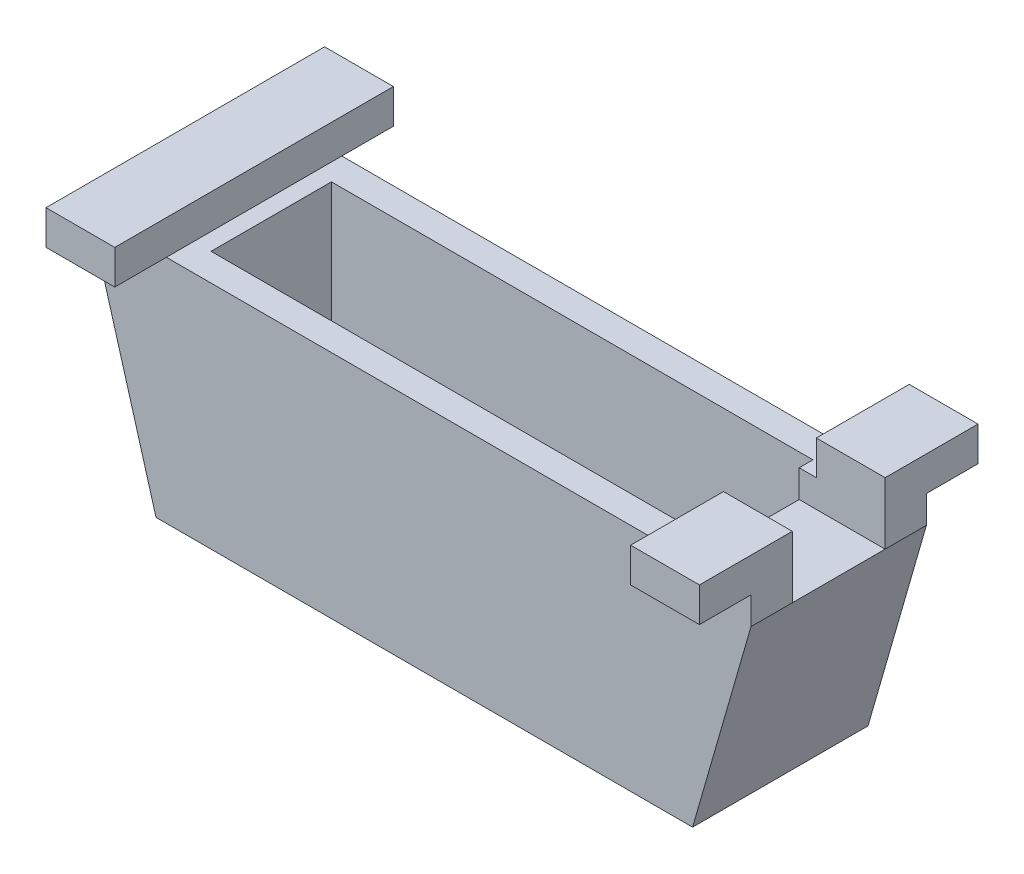
SolidWorks part; units mm, degrees
material "6061-T6 (SS)"
ref_plane "Front Plane" through (0, 0, 0) normal (0, 0, 1) x (1, 0, 0)
ref_plane "Top Plane" through (0, 0, 0) normal (0, 1, 0) x (1, 0, 0)
ref_plane "Right Plane" through (0, 0, 0) normal (1, 0, 0) x (0, 0, -1)
sketch "Sketch1" plane through (0, 0, 0) normal (0, 1, 0) x (1, 0, 0)
  line L1 (-44.45, -11.1125) -> (44.45, -11.1125)
  line L2 (-44.45, -11.1125) -> (-44.45, 11.1125)
  line L3 (-44.45, 11.1125) -> (44.45, 11.1125)
  line L4 (44.45, -11.1125) -> (44.45, 11.1125)
  line L5 (-44.45, -11.1125) -> (44.45, 11.1125) construction
  line L6 (-44.45, 11.1125) -> (44.45, -11.1125) construction
  point P0 (0, 0)
  dimension "D1" = 22.225
  dimension "D2" = 88.9
extrude "Boss-Extrude1" add sketch "Sketch1" along normal blind 2.54
sketch "Sketch2" plane through (0, 2.54, 0) normal (0, 1, 0) x (1, 0, 0)
  line L1 (44.45, -11.1125) -> (-44.45, -11.1125)
  line L2 (44.45, -11.1125) -> (44.45, 11.1125)
  line L3 (44.45, 11.1125) -> (-44.45, 11.1125)
  line L4 (-44.45, -11.1125) -> (-44.45, 11.1125)
  line L5 (44.45, -11.1125) -> (-44.45, 11.1125) construction
  line L6 (44.45, 11.1125) -> (-44.45, -11.1125) construction
  line L7 (49.53, -16.1925) -> (-49.53, -16.1925)
  line L8 (49.53, -16.1925) -> (49.53, 16.1925)
  line L9 (49.53, 16.1925) -> (-49.53, 16.1925)
  line L10 (-49.53, -16.1925) -> (-49.53, 16.1925)
  line L11 (49.53, -16.1925) -> (-49.53, 16.1925) construction
  line L12 (49.53, 16.1925) -> (-49.53, -16.1925) construction
  point P0 (0, 0)
  point P7 (0, 0)
  dimension "D1" = 5.08
  dimension "D2" = 5.08
extrude "Boss-Extrude3" add sketch "Sketch2" along normal blind 34.925 and the other way up to surface (2.54 mm away) other way up to face at (0, 0, 0)
sketch "Sketch4" plane through (0, 37.465, 0) normal (0, 1, 0) x (1, 0, 0)
  line L0 (-49.53, -16.1925) -> (49.53, -16.1925) construction
  line L1 (-44.45, 11.1125) -> (44.45, 11.1125)
  line L2 (-44.45, 11.1125) -> (-44.45, -11.1125)
  line L3 (-44.45, -11.1125) -> (44.45, -11.1125)
  line L4 (44.45, 11.1125) -> (44.45, -11.1125)
  line L5 (-44.45, 11.1125) -> (44.45, -11.1125) construction
  line L6 (-44.45, -11.1125) -> (44.45, 11.1125) construction
  line L7 (-60.3178, 16.1925) -> (60.3178, 16.1925)
  line L8 (-60.3178, 16.1925) -> (-60.3178, -16.1925)
  line L9 (-60.3178, -16.1925) -> (60.3178, -16.1925)
  line L10 (60.3178, 16.1925) -> (60.3178, -16.1925)
  line L11 (-60.3178, 16.1925) -> (60.3178, -16.1925) construction
  line L12 (-60.3178, -16.1925) -> (60.3178, 16.1925) construction
  point P0 (0, 0)
  point P7 (0, 0)
extrude "Boss-Extrude4" add sketch "Sketch4" along normal blind 5.08
sketch "Sketch5" plane through (0, 42.545, 0) normal (0, 1, 0) x (1, 0, 0)
  line L0 (-60.3178, -16.1925) -> (60.3178, -16.1925) construction
  line L1 (60.3178, 25.7175) -> (47.6178, 25.7175)
  line L2 (60.3178, 25.7175) -> (60.3178, -25.7175)
  line L3 (60.3178, -25.7175) -> (47.6178, -25.7175)
  line L4 (47.6178, 25.7175) -> (47.6178, -25.7175)
  line L5 (60.3178, 16.1925) -> (-60.3178, 16.1925) construction
  line L6 (0, -16.1925) -> (0, 16.1925) construction
  line L7 (-47.6178, 25.7175) -> (-47.6178, -25.7175)
  line L8 (-60.3178, -25.7175) -> (-47.6178, -25.7175)
  line L9 (-60.3178, 25.7175) -> (-60.3178, -25.7175)
  line L10 (-60.3178, 25.7175) -> (-47.6178, 25.7175)
  line L11 (60.3178, -16.1925) -> (60.3178, 16.1925) construction
  dimension "D1" = 12.7
  dimension "D3" = 9.525
  dimension "D4" = 9.525
extrude "Boss-Extrude5" add sketch "Sketch5" along normal blind 6.35
sketch "Sketch6" plane through (0, 0, -16.1925) normal (0, 0, -1) x (-1, 0, 0)
  line L0 (-49.53, 0) -> (-60.3178, 37.465)
  line L1 (-60.3178, 37.465) -> (-49.53, 37.465)
  line L2 (-49.53, 37.465) -> (-49.53, 0)
  line L3 (49.53, 37.465) -> (60.3178, 37.465)
  line L4 (60.3178, 37.465) -> (49.53, 0)
  line L5 (49.53, 0) -> (49.53, 37.465)
extrude "Boss-Extrude6" add sketch "Sketch6" against normal up to surface (32.385 mm away) up to face at (0, 32.004, 16.1925)
sketch "Sketch7" plane through (0, 48.895, 0) normal (0, 1, 0) x (1, 0, 0)
  line L1 (44.45, -8.5725) -> (60.3178, -8.5725)
  line L2 (44.45, -8.5725) -> (44.45, 8.5725)
  line L3 (44.45, 8.5725) -> (60.3178, 8.5725)
  line L4 (60.3178, -8.5725) -> (60.3178, 8.5725)
  line L5 (60.3178, -25.7175) -> (60.3178, 25.7175) construction
  line L6 (44.45, -11.1125) -> (44.45, 11.1125) construction
  point P4 (0, 0)
  point P8 (60.3178, 0)
  point P9 (60.3178, 0)
  point P10 (0, 0)
  dimension "D1" = 17.145
extrude "Cut-Extrude1" cut sketch "Sketch7" against normal blind 11.43
equation "\"D1@Sketch1\"=0.875in"
